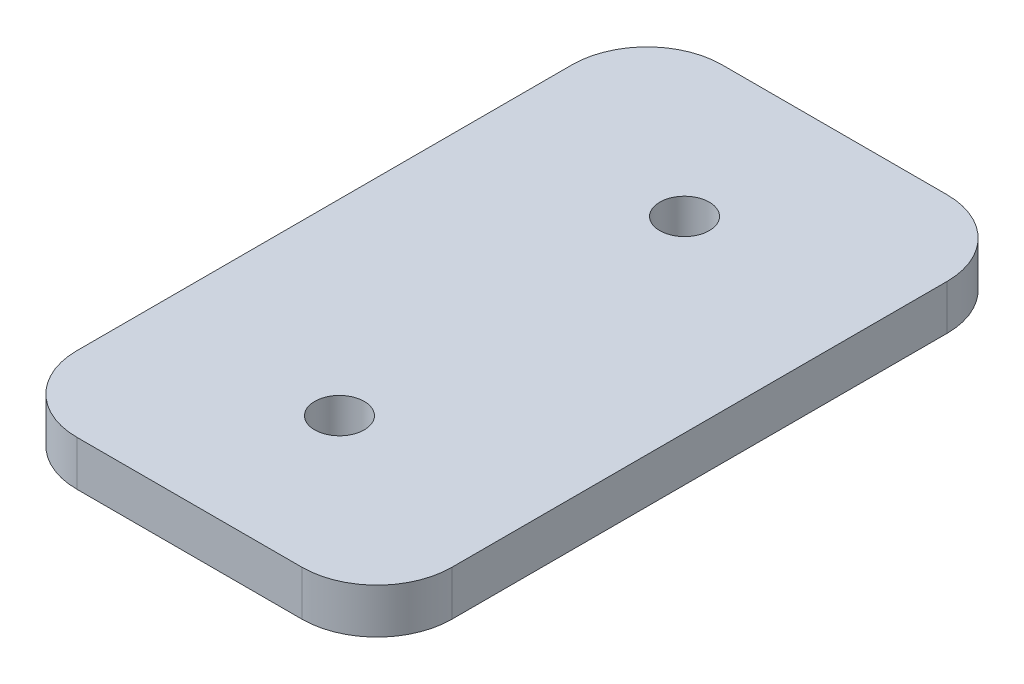
SolidWorks part; units mm, degrees
material "Plain Carbon Steel"
ref_plane "Front Plane" through (0, 0, 0) normal (0, 0, 1) x (1, 0, 0)
ref_plane "Top Plane" through (0, 0, 0) normal (0, 1, 0) x (1, 0, 0)
ref_plane "Right Plane" through (0, 0, 0) normal (1, 0, 0) x (0, 0, -1)
sketch "Sketch1" plane through (0, 0, 0) normal (0, 0, 1) x (1, 0, 0)
  line L0 (491.9747, 0) -> (250.4874, 0) construction
  line L1 (371.2311, 0) -> (371.2311, 25) construction
  line L3 (396.2311, 19) -> (346.2311, 19)
  line L4 (396.2311, 19) -> (396.2311, 25)
  line L5 (396.2311, 25) -> (346.2311, 25)
  line L6 (346.2311, 19) -> (346.2311, 25)
  line L7 (396.2311, 19) -> (346.2311, 25) construction
  line L8 (396.2311, 25) -> (346.2311, 19) construction
  point P6 (371.2311, 22)
  dimension "D1" = 25
  dimension "D2" = 6
  dimension "D3" = 50
extrude "Boss-Extrude1" add sketch "Sketch1" along normal blind 40 and the other way blind 46
sketch "Sketch2" plane through (0, 19, 0) normal (0, -1, 0) x (1, 0, 0)
  line L0 (371.2311, -46) -> (371.2311, 40) construction
  line L1 (346.2311, -46) -> (396.2311, -46) construction
  line L2 (346.2311, 40) -> (396.2311, 40) construction
  line L3 (371.2311, -3) -> (318.041, -3) construction
  circle A0 centre (371.2311, -26) radius 3.3
  circle A1 centre (371.2311, 20) radius 3.3
  dimension "D1" = 6.6
  dimension "D2" = 46
extrude "Cut-Extrude1" cut sketch "Sketch2" against normal through all
fillet "Fillet1" radius 10 4 edges at (346.2311, 22, -46) (396.2311, 22, -46) (346.2311, 22, 40) (396.2311, 22, 40)
